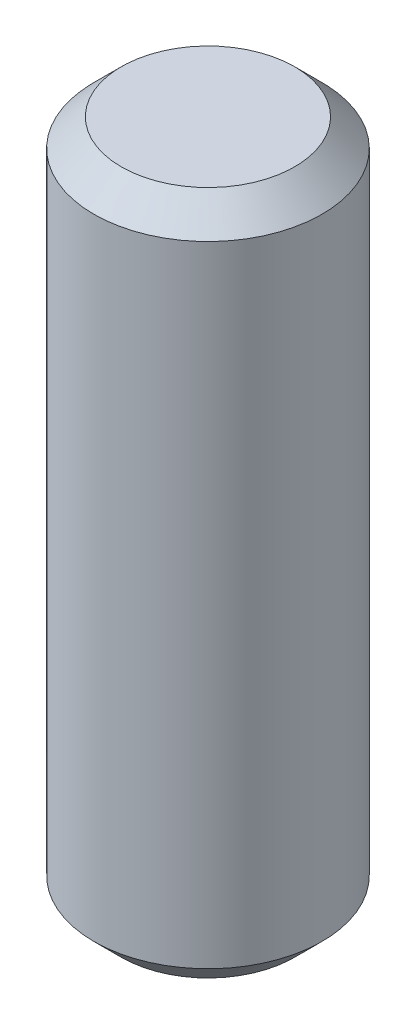
SolidWorks part; units mm, degrees
ref_plane "Front Plane" through (0, 0, 0) normal (0, 0, 1) x (1, 0, 0)
ref_plane "Top Plane" through (0, 0, 0) normal (0, 1, 0) x (1, 0, 0)
ref_plane "Right Plane" through (0, 0, 0) normal (1, 0, 0) x (0, 0, -1)
sketch "Sketch1" plane through (0, 0, 0) normal (0, 1, 0) x (1, 0, 0)
  circle A0 centre (0, 0) radius 6.35
  dimension "D1" = 12.7
extrude "Boss-Extrude1" add sketch "Sketch1" along normal mid plane 38.1 contours A0
chamfer "Chamfer1" distance 1.524 angle 45 2 edges at (0, -19.05, 6.35) (0, 19.05, 6.35)
